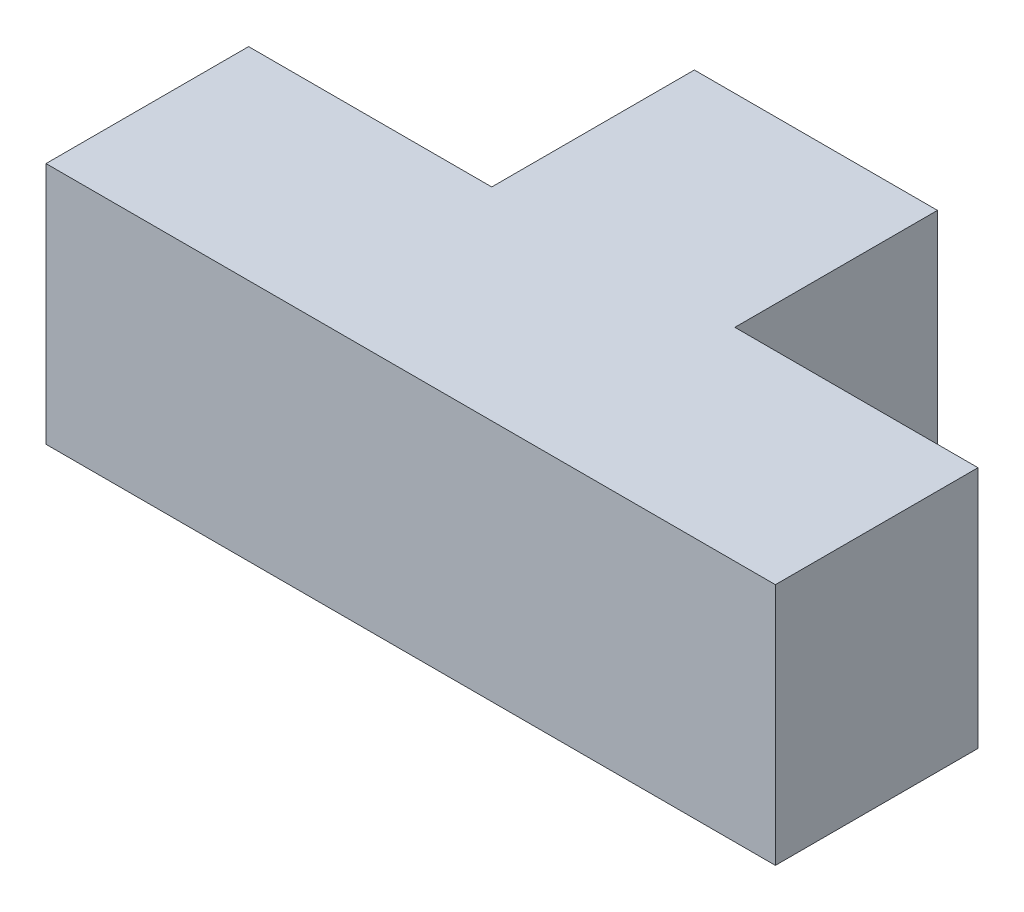
SolidWorks part; units mm, degrees
ref_plane "Front" through (0, 0, 0) normal (0, 0, 1) x (1, 0, 0)
ref_plane "Top" through (0, 0, 0) normal (0, 1, 0) x (1, 0, 0)
ref_plane "Right" through (0, 0, 0) normal (1, 0, 0) x (0, 0, -1)
sketch "Sketch1" plane through (0, 0, 0) normal (0, 1, 0) x (1, 0, 0)
  line L0 (30, 50) -> (60, 50)
  line L1 (60, 50) -> (60, 25)
  line L2 (60, 25) -> (90, 25)
  line L3 (90, 25) -> (90, 0)
  line L4 (90, 0) -> (0, 0)
  line L5 (0, 0) -> (0, 25)
  line L6 (0, 25) -> (30, 25)
  line L7 (30, 25) -> (30, 50)
  point P2 (0, 0)
  dimension "D1" = 30
  dimension "D2" = 25
  dimension "D3" = 25
extrude "Boss-Extrude1" add sketch "Sketch1" along normal blind 30
